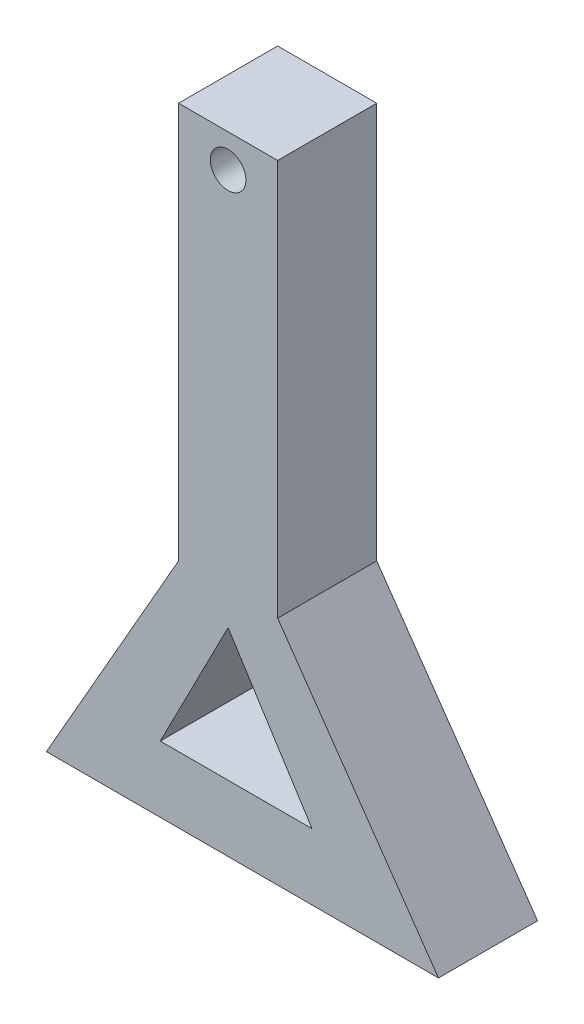
SolidWorks part; units mm, degrees
ref_plane "Alzado" through (0, 0, 0) normal (0, 0, 1) x (1, 0, 0)
ref_plane "Planta" through (0, 0, 0) normal (0, 1, 0) x (1, 0, 0)
ref_plane "Vista lateral" through (0, 0, 0) normal (1, 0, 0) x (0, 0, -1)
sketch "Croquis1" plane through (0, 0, 0) normal (0, 0, 1) x (1, 0, 0)
  line L0 (-7.5, 0) -> (-27.5, -35)
  line L1 (-7.5, -35) -> (11.8438, -35)
  line L2 (-7.5, 0) -> (-7.5, 34.8651)
  line L3 (-7.5, 34.8651) -> (7.5, 34.8651)
  line L4 (7.5, 0) -> (7.5, 34.8651)
  line L5 (0, 0) -> (7.5, 34.8651) construction
  line L6 (-7.5, 34.8651) -> (0, 0) construction
  line L7 (-27.5, -35) -> (-7.5, -35)
  line L8 (7.5, 0) -> (31.8438, -35)
  line L9 (11.8438, -35) -> (31.8438, -35)
  line L10 (-10.2682, -25) -> (0, -5)
  line L11 (0, -5) -> (12.7074, -25)
  line L12 (-10.2682, -25) -> (12.7074, -25)
  point P0 (0, 0)
  dimension "D1" = 15
  dimension "D2" = 70
  dimension "D3" = 20
  dimension "D4" = 20
  dimension "D5" = 30
  dimension "D6" = 10
  dimension "D7" = 10
  dimension "D8" = 10
  dimension "D9" = 10
  dimension "D10" = 22.9756
  dimension "D11" = 34.8651
  dimension "D12" = 34.8651
  dimension "D13" = 7.5
extrude "Saliente-Extruir1" add sketch "Croquis1" along normal blind 10
sketch "Croquis2" plane through (0, 0, 10) normal (0, 0, 1) x (1, 0, 0)
  line L1 (-7.5, 34.8651) -> (-7.5, 0) construction
  line L3 (7.5, 34.8651) -> (-7.5, 34.8651) construction
  circle A0 centre (0, 28.8651) radius 2.5
  dimension "D1" = 5
  dimension "D2" = 7.5
  dimension "D3" = 6
extrude "Cortar-Extruir1" cut sketch "Croquis2" against normal blind 10
sketch "Croquis4" plane through (0, 0, 10) normal (0, 0, 1) x (1, 0, 0)
  line L1 (7.5, 0) -> (-7.5, 0)
  line L2 (7.5, 0) -> (7.5, 60)
  line L3 (7.5, 60) -> (-7.5, 60)
  line L4 (-7.5, 0) -> (-7.5, 60)
  dimension "D1" = 60
extrude "Saliente-Extruir2" add sketch "Croquis4" against normal blind 15
sketch "Croquis5" plane through (0, 0, 10) normal (0, 0, 1) x (1, 0, 0)
  line L0 (-27.5, -35) -> (-0.7347, 11.8393)
  line L1 (-0.7347, 11.8393) -> (31.8438, -35)
  line L3 (-7.5, 0) -> (-27.5, -35) construction
  line L4 (-10.2682, -25) -> (12.7074, -25)
  line L5 (12.7074, -25) -> (0, -5)
  line L6 (0, -5) -> (-10.2682, -25)
  line M3 (31.8438, -35) -> (7.5, 0)
  line M7 (-7.5, 0) -> (-27.5, -35)
  line M8 (-27.5, -35) -> (31.8438, -35)
  line M9 (12.7074, -25) -> (-10.2682, -25)
  line M10 (-10.2682, -25) -> (0, -5)
  line M11 (0, -5) -> (12.7074, -25)
  dimension "D1" = 0
  dimension "D2" = 0
extrude "Saliente-Extruir3" add sketch "Croquis5" against normal blind 15 contours L1 L0 M7 M8 M3 M11 M9 M10
sketch "Croquis6" plane through (0, 0, 10) normal (0, 0, 1) x (1, 0, 0)
  line L0 (7.5, 60) -> (-7.5, 60) construction
  circle A0 centre (0, 55) radius 2.7
  dimension "D1" = 5.4
  dimension "D2" = 5
extrude "Cortar-Extruir2" cut sketch "Croquis6" against normal blind 15
